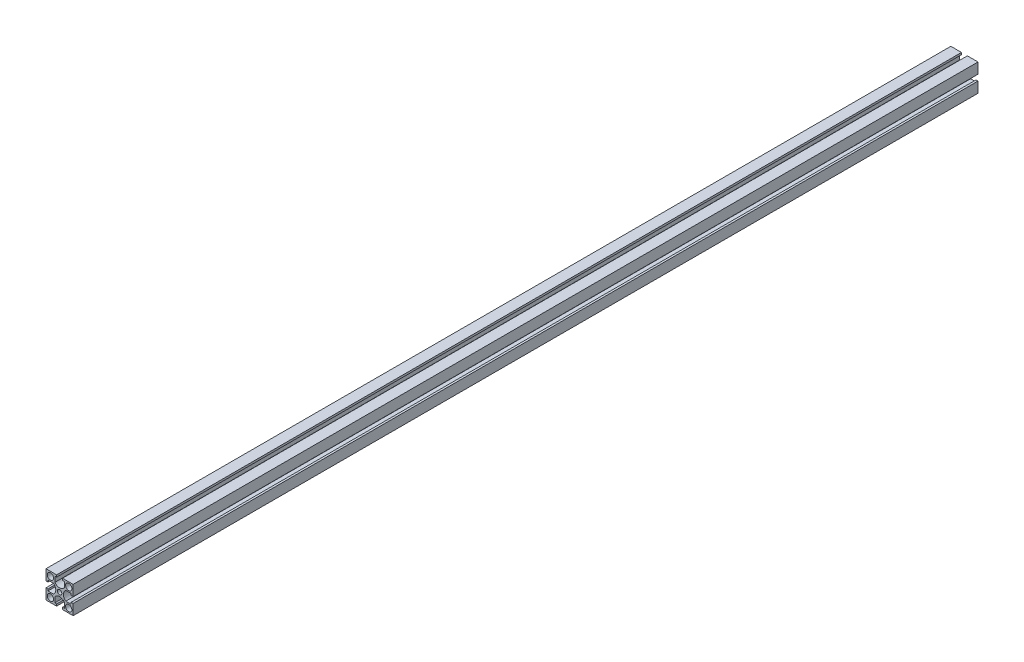
SolidWorks part; units mm, degrees
material "6063 T5"
ref_plane "Спереди" through (0, 0, 0) normal (0, 0, 1) x (1, 0, 0)
ref_plane "Сверху" through (0, 0, 0) normal (0, 1, 0) x (1, 0, 0)
ref_plane "Справа" through (0, 0, 0) normal (1, 0, 0) x (0, 0, -1)
sketch "Эскиз1" plane through (0, 0, 0) normal (0, 0, 1) x (1, 0, 0)
  line L0 (11.3549, 30.3863) -> (41.3549, 30.3863) construction
  line L10 (-15, 0) -> (15, 0) construction
  line L11 (-15, 5.2) -> (-15, 15)
  line L12 (-15, 15) -> (-5.2, 15)
  line L14 (5.2, 15) -> (15, 15)
  line L15 (15, 15) -> (15, 5.2)
  line L16 (15, -5.2) -> (15, -15)
  line L17 (15, -15) -> (5.2, -15)
  line L18 (-5.2, -15) -> (-15, -15)
  line L19 (-15, -15) -> (-15, -5.2)
  line L21 (10.1, -10.1) -> (-10.1, -10.1) construction
  line L22 (10.1, -10.1) -> (10.1, 10.1) construction
  line L23 (10.1, 10.1) -> (-10.1, 10.1) construction
  line L24 (-10.1, -10.1) -> (-10.1, 10.1) construction
  line L25 (10.1, -10.1) -> (-10.1, 10.1) construction
  line L26 (10.1, 10.1) -> (-10.1, -10.1) construction
  circle A0 centre (-10.1, 10.1) radius 3.5
  circle A1 centre (10.1, 10.1) radius 3.5
  circle A2 centre (-10.1, -10.1) radius 3.5
  circle A3 centre (10.1, -10.1) radius 3.5
  circle A4 centre (0, 0) radius 2.5
  point P4 (0, 0)
  point P17 (0, 0)
  line B0 (-15, 5.2) -> (-15, 3.25)
  line B1 (-15, 3.25) -> (-12.8, 3.25)
  line B2 (-12.8, 3.25) -> (-12.8, 5.2)
  line B3 (-12.8, 5.2) -> (-6.8, 5.2)
  line B4 (-6.8, -5.2) -> (-12.8, -5.2)
  line B5 (-12.8, -5.2) -> (-12.8, -3.25)
  line B6 (-12.8, -3.25) -> (-15, -3.25)
  line B7 (-15, -3.25) -> (-15, -5.2)
  line B8 (-15, 5.2) -> (-15, -5.2) construction
  arc B9 (-6.8, 5.2) -> (-6.8, -5.2) centre (-10.7, 0) cw
  line B10 (5.2, 15) -> (3.25, 15)
  line B11 (3.25, 15) -> (3.25, 12.8)
  line B12 (3.25, 12.8) -> (5.2, 12.8)
  line B13 (5.2, 12.8) -> (5.2, 6.8)
  line B14 (-5.2, 6.8) -> (-5.2, 12.8)
  line B15 (-5.2, 12.8) -> (-3.25, 12.8)
  line B16 (-3.25, 12.8) -> (-3.25, 15)
  line B17 (-3.25, 15) -> (-5.2, 15)
  line B18 (5.2, 15) -> (-5.2, 15) construction
  arc B19 (5.2, 6.8) -> (-5.2, 6.8) centre (0, 10.7) cw
  line B20 (15, -5.2) -> (15, -3.25)
  line B21 (15, -3.25) -> (12.8, -3.25)
  line B22 (12.8, -3.25) -> (12.8, -5.2)
  line B23 (12.8, -5.2) -> (6.8, -5.2)
  line B24 (6.8, 5.2) -> (12.8, 5.2)
  line B25 (12.8, 5.2) -> (12.8, 3.25)
  line B26 (12.8, 3.25) -> (15, 3.25)
  line B27 (15, 3.25) -> (15, 5.2)
  line B28 (15, -5.2) -> (15, 5.2) construction
  arc B29 (6.8, -5.2) -> (6.8, 5.2) centre (10.7, 0) cw
  line B30 (-5.2, -15) -> (-3.25, -15)
  line B31 (-3.25, -15) -> (-3.25, -12.8)
  line B32 (-3.25, -12.8) -> (-5.2, -12.8)
  line B33 (-5.2, -12.8) -> (-5.2, -6.8)
  line B34 (5.2, -6.8) -> (5.2, -12.8)
  line B35 (5.2, -12.8) -> (3.25, -12.8)
  line B36 (3.25, -12.8) -> (3.25, -15)
  line B37 (3.25, -15) -> (5.2, -15)
  line B38 (-5.2, -15) -> (5.2, -15) construction
  arc B39 (-5.2, -6.8) -> (5.2, -6.8) centre (0, -10.7) cw
  dimension "D5" = 7
  dimension "D6" = 5
  dimension "D1" = 30
  dimension "D2" = 30
  dimension "D3" = 4
  dimension "D4" = 20.2
sketch_block_instance "Блок1-1"
sketch_block "Блок1" parameters "D4"=6.5, "D1"=10.4, "D2"=6.5, "D3"=2.2, "D5"=6
sketch_block_instance "Блок1-2"
sketch_block_instance "Блок1-3"
sketch_block_instance "Блок1-4"
extrude "Бобышка-Вытянуть1" add sketch "Эскиз1" along normal blind 1000 contours B33 B39 B34 B35 B36 B37 L17 L16 B20 B21 B22 B23 B29 B24 B25 B26 B27 L15 L14 B10 B11 B12 B13 B19 B14 B15 B16 B17 L12 L11 B0 B1 B2 B3 B9 B4 B5 B6 B7 L19 L18 B30 B31 B32 A0 A1 A2
